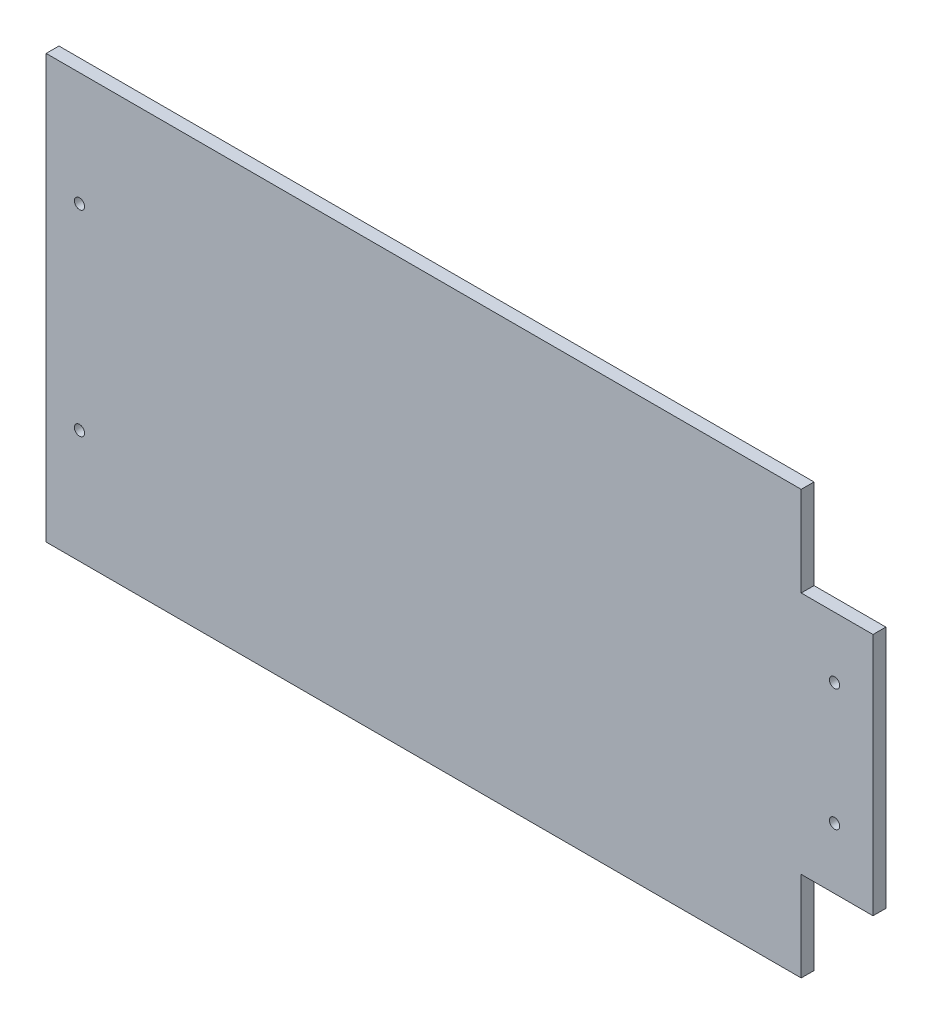
SolidWorks part; units mm, degrees
ref_plane "Front Plane" through (0, 0, 0) normal (0, 0, 1) x (1, 0, 0)
ref_plane "Top Plane" through (0, 0, 0) normal (0, 1, 0) x (1, 0, 0)
ref_plane "Right Plane" through (0, 0, 0) normal (1, 0, 0) x (0, 0, -1)
sketch "Sketch1" plane through (0, 0, 0) normal (0, 0, 1) x (1, 0, 0)
  line L8 (-171.8023, 0) -> (198.6628, 0) construction
  line L9 (-164.2209, -82.5) -> (-164.2209, 82.5)
  line L10 (-164.2209, 82.5) -> (130.1791, 82.5)
  line L11 (130.1791, 82.5) -> (130.1791, 47.5)
  line L12 (130.1791, 47.5) -> (158.1791, 47.5)
  line L13 (158.1791, 47.5) -> (158.1791, -47.5)
  line L14 (130.1791, -47.5) -> (158.1791, -47.5)
  line L15 (130.1791, -82.5) -> (130.1791, -47.5)
  line L16 (-164.2209, -82.5) -> (130.1791, -82.5)
  point P9 (158.1791, 0)
  point P13 (-164.2209, 0)
  dimension "D1" = 35
  dimension "D2" = 47.5
  dimension "D3" = 294.4
  dimension "D4" = 28
extrude "Boss-Extrude1" add sketch "Sketch1" along normal blind 5
sketch "Sketch2" plane through (0, 0, 5) normal (0, 0, 1) x (1, 0, 0)
  line L0 (-164.2209, 93.7319) -> (-164.2209, -107.0542) construction
  line L1 (-164.2209, 82.5) -> (-164.2209, -82.5) construction
  line L2 (-151.2209, 96.9039) -> (-151.2209, -110.5434) construction
  line L3 (130.1791, 82.5) -> (-164.2209, 82.5) construction
  line L4 (-164.2209, -82.5) -> (130.1791, -82.5) construction
  line L5 (143.1791, 56.7784) -> (143.1791, -71.3695) construction
  line L7 (158.1791, 47.5) -> (130.1791, 47.5) construction
  line L8 (130.1791, -47.5) -> (158.1791, -47.5) construction
  line L9 (158.1791, -47.5) -> (158.1791, 47.5) construction
  circle A0 centre (-151.2209, 38.25) radius 2
  circle A1 centre (-151.2209, -38.25) radius 2
  circle A2 centre (143.1791, 23.75) radius 2
  circle A3 centre (143.1791, -23.75) radius 2
  dimension "D2" = 4
  dimension "D6" = 4
  dimension "D7" = 23.75
  dimension "D1" = 13
  dimension "D3" = 44.25
  dimension "D4" = 44.25
  dimension "D5" = 15
  dimension "D8" = 23.75
extrude "Cut-Extrude1" cut sketch "Sketch2" against normal blind 10
